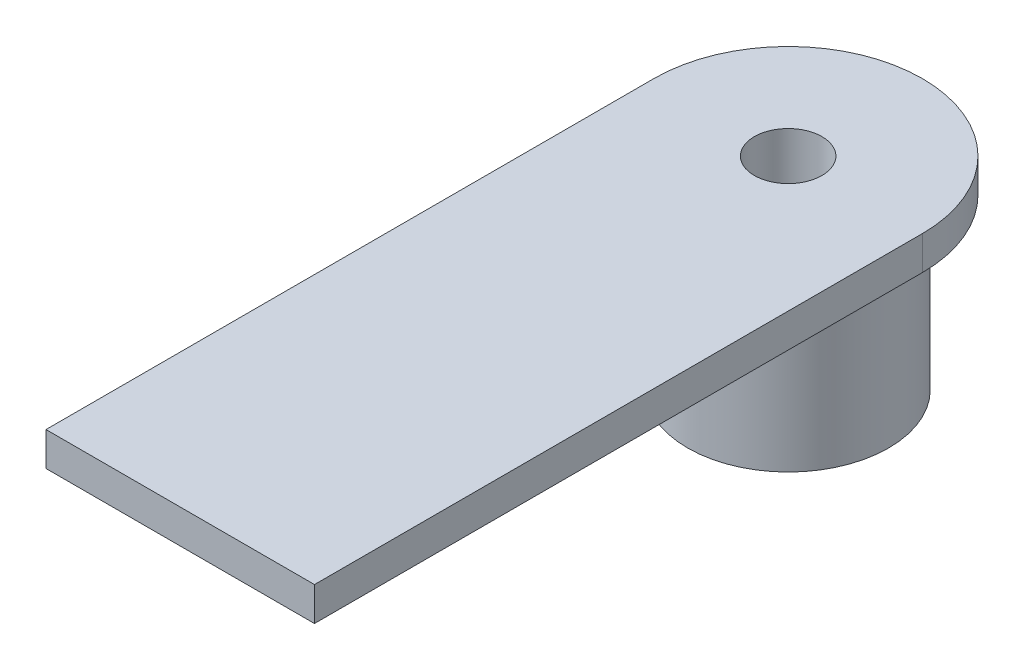
SolidWorks part; units mm, degrees
ref_plane "Front Plane" through (0, 0, 0) normal (0, 0, 1) x (1, 0, 0)
ref_plane "Top Plane" through (0, 0, 0) normal (0, 1, 0) x (1, 0, 0)
ref_plane "Right Plane" through (0, 0, 0) normal (1, 0, 0) x (0, 0, -1)
sketch "Sketch1" plane through (0, 0, 0) normal (0, 1, 0) x (1, 0, 0)
  circle A0 centre (0, 0) radius 5.95
  dimension "D1" = 11.9
extrude "Boss-Extrude1" add sketch "Sketch1" along normal blind 10
sketch "Sketch2" plane through (0, 10, 0) normal (0, 1, 0) x (1, 0, 0)
  line L2 (-7.95, 0) -> (-7.95, -16)
  line L3 (-7.95, -16) -> (7.95, -16)
  line L4 (7.95, 0) -> (7.95, -16)
  arc A0 (7.95, 0) -> (-7.95, 0) centre (0, 0) ccw
  circle A1 centre (0, 0) radius 5.95 construction
  dimension "D1" = 2
  dimension "D2" = 16
extrude "Boss-Extrude2" add sketch "Sketch2" along normal blind 2
chamfer "Chamfer1" distance 1.5 angle 13 1 edges at (0, 10, 5.95)
sketch "Sketch3" plane through (0, 0, 0) normal (0, -1, 0) x (1, 0, 0)
  circle A0 centre (0, 0) radius 2
  dimension "D1" = 4
extrude "Cut-Extrude1" cut sketch "Sketch3" against normal through all
sketch "Sketch4" plane through (0, 0, 16) normal (0, 0, 1) x (1, 0, 0)
  line L1 (-7.95, 12) -> (7.95, 12)
  line L2 (-7.95, 12) -> (-7.95, 10)
  line L3 (-7.95, 10) -> (7.95, 10)
  line L4 (7.95, 12) -> (7.95, 10)
extrude "Boss-Extrude3" add sketch "Sketch4" along normal blind 20
